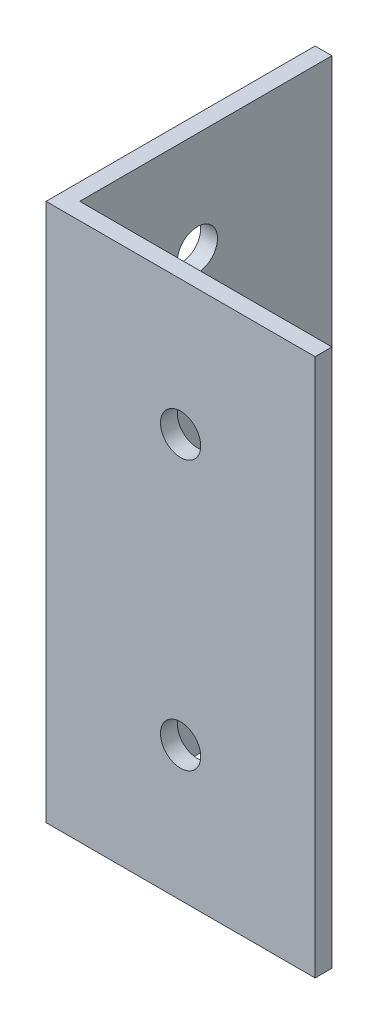
SolidWorks part; units mm, degrees
material "6061-T6 (SS)"
ref_plane "Front Plane" through (0, 0, 0) normal (0, 0, 1) x (1, 0, 0)
ref_plane "Top Plane" through (0, 0, 0) normal (0, 1, 0) x (1, 0, 0)
ref_plane "Right Plane" through (0, 0, 0) normal (1, 0, 0) x (0, 0, -1)
sketch "Sketch1" plane through (0, 0, 0) normal (0, 1, 0) x (1, 0, 0)
  line L0 (0, 25.4) -> (1.5875, 25.4)
  line L1 (1.5875, 25.4) -> (1.5875, 1.5875)
  line L2 (1.5875, 1.5875) -> (25.4, 1.5875)
  line L3 (25.4, 1.5875) -> (25.4, 0)
  line L4 (25.4, 0) -> (0, 0)
  line L5 (0, 0) -> (0, 25.4)
  dimension "D1" = 1.5875
  dimension "D2" = 25.4
extrude "Boss-Extrude1" add sketch "Sketch1" along normal blind 50.8
hole_wizard "#6 Clearance Hole1" positions "Sketch3" profile "Sketch2" hole size "#6" standard "ANSI Inch" end condition through all
sketch "Sketch3" plane through (0, 0, -1.5875) normal (0, 0, -1) x (-1, 0, 0)
  line L0 (-25.4, 50.8) -> (-25.4, 0) construction
  line L2 (-25.4, 50.8) -> (-1.5875, 50.8) construction
  line L3 (-25.4, 0) -> (-1.5875, 0) construction
  point P0 (-12.7, 38.1)
  point P2 (-12.7, 12.7)
  dimension "D1" = 12.7
  dimension "D2" = 12.7
  dimension "D3" = 12.7
  dimension "D4" = 12.7
sketch "Sketch2" plane through (12.7, 38.1, -1.5875) normal (1, 0, 0) x (0, 1, 0)
  line L0 (0, 0) -> (0, 1.5875)
  line L1 (0, 1.5875) -> (1.8986, 1.5875)
  line L2 (1.8986, 1.5875) -> (1.8986, 0)
  line L5 (1.8986, 0) -> (0, 0)
  line L11 (0, -6.35) -> (0, 107.95) construction
  dimension "Thru Hole Dia." = 3.7973
  dimension "Thru Hole Depth" = 1.5875
hole_wizard "#6 Clearance Hole2" positions "Sketch5" profile "Sketch4" hole size "#6" standard "ANSI Inch" end condition through all
sketch "Sketch5" plane through (1.5875, 0, 0) normal (1, 0, 0) x (0, 0, -1)
  line L0 (1.5875, 0) -> (25.4, 0) construction
  line L2 (25.4, 50.8) -> (25.4, 0) construction
  line L3 (1.5875, 50.8) -> (25.4, 50.8) construction
  point P0 (12.7, 41.275)
  point P2 (12.7, 9.525)
  dimension "D1" = 9.525
  dimension "D2" = 12.7
  dimension "D3" = 9.525
  dimension "D4" = 12.7
sketch "Sketch4" plane through (1.5875, 41.275, -12.7) normal (0, 1, 0) x (0, 0, -1)
  line L0 (0, 0) -> (0, 1.5875)
  line L1 (0, 1.5875) -> (1.8986, 1.5875)
  line L2 (1.8986, 1.5875) -> (1.8986, 0)
  line L5 (1.8986, 0) -> (0, 0)
  line L11 (0, -6.35) -> (0, 107.95) construction
  dimension "Thru Hole Dia." = 3.7973
  dimension "Thru Hole Depth" = 1.5875
